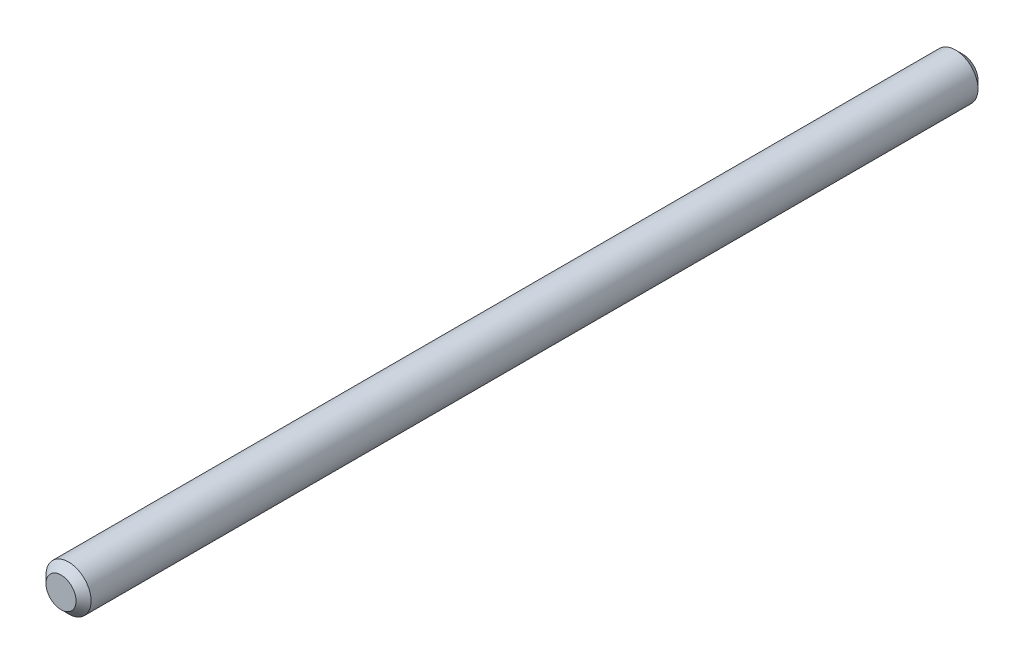
SolidWorks part; units mm, degrees
material "Messing"
ref_plane "Ebene vorne" through (0, 0, 0) normal (0, 0, 1) x (1, 0, 0)
ref_plane "Ebene oben" through (0, 0, 0) normal (0, 1, 0) x (1, 0, 0)
ref_plane "Ebene rechts" through (0, 0, 0) normal (1, 0, 0) x (0, 0, -1)
sketch "Skizze1" plane through (0, 0, 0) normal (0, 0, 1) x (1, 0, 0)
  circle A0 centre (0, 0) radius 1.5
  dimension "D1" = 3
extrude "Aufsatz-Linear austragen1" add sketch "Skizze1" along normal mid plane 60
chamfer "Fase1" distance 0.5 angle 45 2 edges at (1.5, 0, -30) (1.5, 0, 30)
